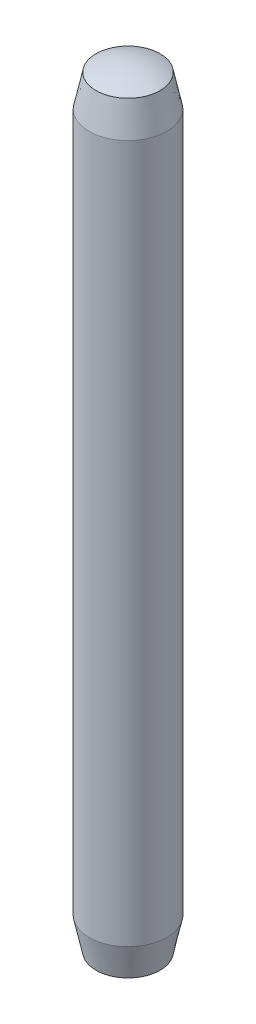
SolidWorks part; units mm, degrees
ref_plane "Front Plane" through (0, 0, 0) normal (0, 0, 1) x (1, 0, 0)
ref_plane "Top Plane" through (0, 0, 0) normal (0, 1, 0) x (1, 0, 0)
ref_plane "Right Plane" through (0, 0, 0) normal (1, 0, 0) x (0, 0, -1)
sketch "Sketch1" plane through (0, 0, 0) normal (0, 1, 0) x (1, 0, 0)
  circle A0 centre (0, 0) radius 0.5
  dimension "D1" = 1
extrude "Boss-Extrude1" add sketch "Sketch1" along normal blind 10
sketch "Sketch2" plane through (0, 0, 0) normal (0, 0, 1) x (1, 0, 0)
  line L0 (0, 0) -> (0, 10) construction
  line L1 (0.5, 10) -> (-0.5, 10) construction
  line L3 (0.5, 0) -> (0.5, 10) construction
  line L4 (0.5, 9.866) -> (0, 9.866) construction
  line L5 (0.5, 9.866) -> (0.5, 10.1)
  line L7 (0, 10) -> (0, 10.1)
  line L8 (0.5, 10.1) -> (-0.5, 10.1)
  line L9 (0.5, 10.1) -> (0, 10.1)
  line L10 (0, 5) -> (1.533, 5) construction
  line L11 (0.5, 0.134) -> (0, 0.134) construction
  line L12 (0.5, -0.1) -> (0, -0.1)
  line L13 (0, 0) -> (0, -0.1)
  line L14 (0.5, 0.134) -> (0.5, -0.1)
  arc A0 (0, 10) -> (0.5, 9.866) centre (0, 9) cw
  arc A1 (0, 0) -> (0.5, 0.134) centre (0, 1) ccw
  dimension "D1" = 1
  dimension "D2" = 0.1
revolve "Cut-Revolve2" cut sketch "Sketch2" angle 360 about L0
sketch "Sketch3" plane through (0, 0, 0) normal (0, 0, 1) x (1, 0, 0)
  line L0 (-0.5, 9.5) -> (-0.4127, 9.9109)
  line L1 (-0.5, 9.866) -> (-0.5, 0.134) construction
  line L2 (-0.5, 9.866) -> (-0.5, 9.5)
  line L3 (0, 0) -> (0, 10) construction
  line L4 (0, 5) -> (0.5, 5) construction
  line L5 (0.5, 0.134) -> (0.5, 9.866) construction
  line L6 (-0.5, 0.134) -> (-0.5, 0.5)
  line L7 (-0.5, 0.5) -> (-0.4127, 0.0891)
  arc A0 (0, 10) -> (-0.5, 9.866) centre (0, 9) ccw construction
  arc A1 (-0.4127, 9.9109) -> (-0.5, 9.866) centre (0, 9) ccw
  arc A2 (-0.4127, 0.0891) -> (-0.5, 0.134) centre (0, 1) cw
  dimension "D1" = 12
  dimension "D2" = 0.5
revolve "Cut-Revolve3" cut sketch "Sketch3" angle 360 about L3
